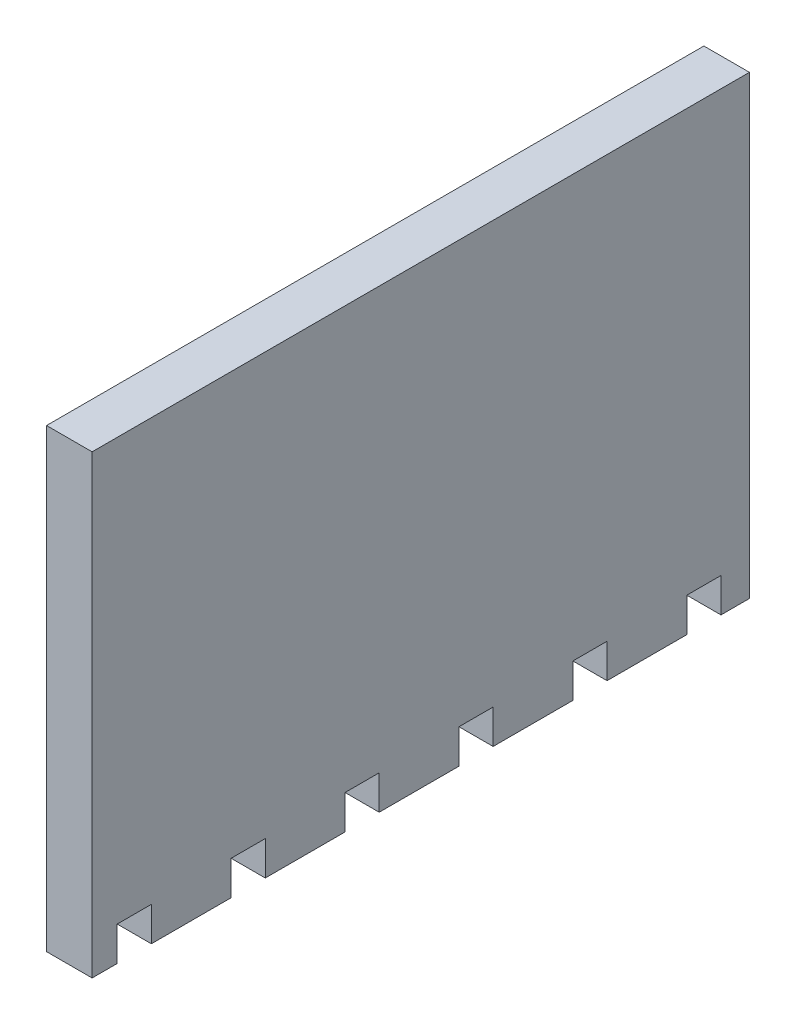
SolidWorks part; units mm, degrees
ref_plane "Front" through (0, 0, 0) normal (0, 0, 1) x (1, 0, 0)
ref_plane "Top" through (0, 0, 0) normal (0, 1, 0) x (1, 0, 0)
ref_plane "Right" through (0, 0, 0) normal (1, 0, 0) x (0, 0, -1)
sketch "Sketch1" plane through (0, 0, 0) normal (0, 0, 1) x (1, 0, 0)
  line L1 (-10, 0) -> (10, 0)
  line L2 (-10, 0) -> (-10, -200)
  line L3 (-10, -200) -> (10, -200)
  line L4 (10, 0) -> (10, -200)
  point P4 (0, 0)
  dimension "D1" = 20
  dimension "D2" = 200
extrude "Boss-Extrude1" add sketch "Sketch1" along normal blind 288.5
sketch "Sketch2" plane through (10, 0, 0) normal (1, 0, 0) x (0, 0, -1)
  line L0 (-288.5, -200) -> (0, -200) construction
  line L1 (-277.5, -185) -> (-262.5, -185)
  line L2 (-277.5, -185) -> (-277.5, -200)
  line L3 (-277.5, -200) -> (-262.5, -200)
  line L4 (-262.5, -185) -> (-262.5, -200)
  line L5 (-288.5, -200) -> (-288.5, 0) construction
  line L6 (-227.5, -185) -> (-212.5, -185)
  line L7 (-227.5, -185) -> (-227.5, -200)
  line L8 (-227.5, -200) -> (-212.5, -200)
  line L9 (-212.5, -185) -> (-212.5, -200)
  line L10 (-177.5, -185) -> (-162.5, -185)
  line L11 (-177.5, -185) -> (-177.5, -200)
  line L12 (-177.5, -200) -> (-162.5, -200)
  line L13 (-162.5, -185) -> (-162.5, -200)
  line L14 (-127.5, -185) -> (-112.5, -185)
  line L15 (-127.5, -185) -> (-127.5, -200)
  line L16 (-127.5, -200) -> (-112.5, -200)
  line L17 (-112.5, -185) -> (-112.5, -200)
  line L18 (-77.5, -185) -> (-62.5, -185)
  line L19 (-77.5, -185) -> (-77.5, -200)
  line L20 (-77.5, -200) -> (-62.5, -200)
  line L21 (-62.5, -185) -> (-62.5, -200)
  line L22 (-27.5, -185) -> (-12.5, -185)
  line L23 (-27.5, -185) -> (-27.5, -200)
  line L24 (-27.5, -200) -> (-12.5, -200)
  line L25 (-12.5, -185) -> (-12.5, -200)
  dimension "D1" = 15
  dimension "D2" = 15
  dimension "D3" = 11
  dimension "D4" = 6
extrude "Cut-Extrude1" cut sketch "Sketch2" against normal up to vertex (20 mm away) up to point (-10, -200, 288.5)
